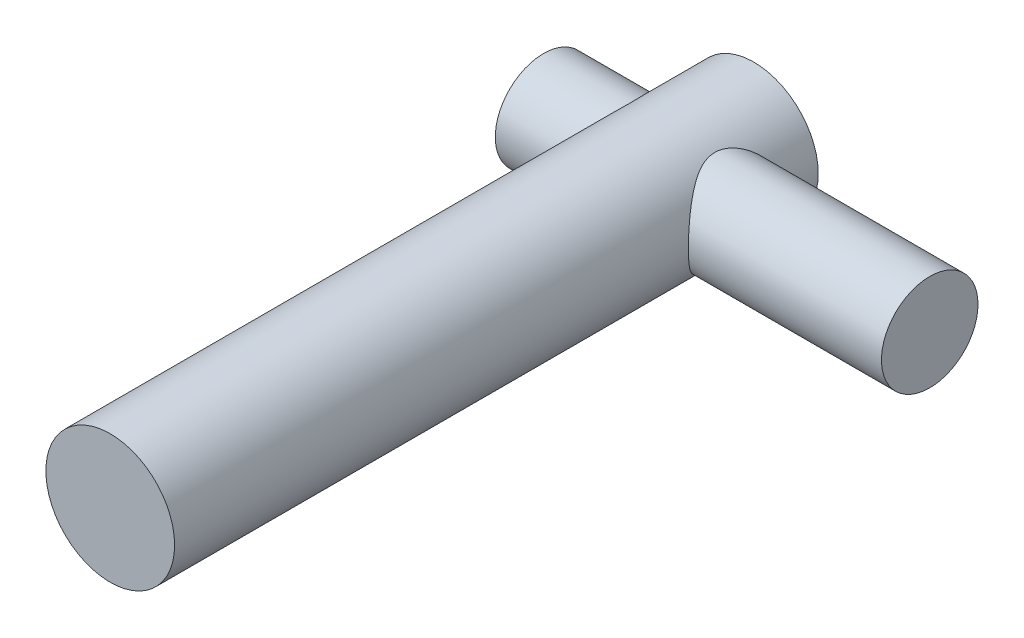
SolidWorks part; units mm, degrees
ref_plane "Alzado" through (0, 0, 0) normal (0, 0, 1) x (1, 0, 0)
ref_plane "Planta" through (0, 0, 0) normal (0, 1, 0) x (1, 0, 0)
ref_plane "Vista lateral" through (0, 0, 0) normal (1, 0, 0) x (0, 0, -1)
sketch "Croquis1" plane through (0, 0, 0) normal (0, 0, 1) x (1, 0, 0)
  circle A0 centre (0, 0) radius 10
  dimension "D1" = 20
extrude "Saliente-Extruir1" add sketch "Croquis1" against normal blind 100
ref_plane "Plano2" through (10, 0, 0) normal (1, 0, 0) x (0, 0, -1)
sketch "Croquis2" plane through (10, 0, 0) normal (1, 0, 0) x (0, 0, -1)
  circle A0 centre (87.3236, 0) radius 7.5
  dimension "D1" = 15
extrude "Saliente-Extruir2" add sketch "Croquis2" against normal mid plane 60
